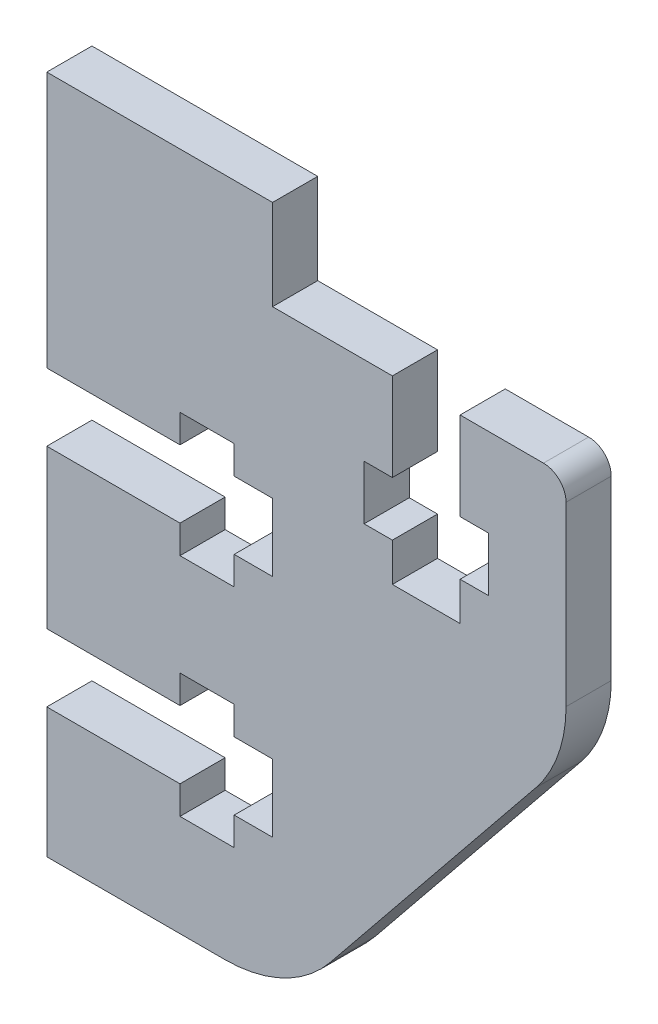
SolidWorks part; units mm, degrees
material "Acrylic (Medium-high impact)"
ref_plane "Front Plane" through (0, 0, 0) normal (0, 0, 1) x (1, 0, 0)
ref_plane "Top Plane" through (0, 0, 0) normal (0, 1, 0) x (1, 0, 0)
ref_plane "Right Plane" through (0, 0, 0) normal (1, 0, 0) x (0, 0, -1)
sketch "Model" plane through (0, 0, 0) normal (0, 0, 1) x (1, 0, 0)
  line L1304 (10, 5.75) -> (8.3, 5.75)
  line L1305 (10, 8.75) -> (8.3, 8.75)
  line L1306 (5.9, 8.75) -> (0, 8.75)
  line L1307 (5.9, 5.75) -> (0, 5.75)
  line L1308 (10, 5.75) -> (10, 8.75)
  line L1309 (10, 26.1) -> (15.306, 26.1)
  line L1310 (18.306, 26.1) -> (22, 26.1)
  line L1311 (21.6642, 13.4853) -> (12.5527, 2.2257)
  line L1312 (23, 25.1) -> (23, 17.2596)
  line L1313 (0, 0) -> (7.8885, 0)
  line L1314 (8.3, 4.5) -> (8.3, 5.75)
  line L1315 (8.3, 8.75) -> (8.3, 10)
  line L1316 (5.9, 4.5) -> (5.9, 5.75)
  line L1317 (5.9, 8.75) -> (5.9, 10)
  line L1318 (8.3, 4.5) -> (5.9, 4.5)
  line L1319 (8.3, 10) -> (5.9, 10)
  line L1320 (10, 15.75) -> (8.3, 15.75)
  line L1321 (10, 18.75) -> (8.3, 18.75)
  line L1322 (5.9, 18.75) -> (0, 18.75)
  line L1323 (5.9, 15.75) -> (0, 15.75)
  line L1324 (10, 15.75) -> (10, 18.75)
  line L1325 (8.3, 14.5) -> (8.3, 15.75)
  line L1326 (8.3, 18.75) -> (8.3, 20)
  line L1327 (5.9, 14.5) -> (5.9, 15.75)
  line L1328 (5.9, 18.75) -> (5.9, 20)
  line L1329 (8.3, 14.5) -> (5.9, 14.5)
  line L1330 (8.3, 20) -> (5.9, 20)
  line L1331 (15.306, 18.1) -> (15.306, 19.8)
  line L1332 (18.306, 18.1) -> (18.306, 19.8)
  line L1333 (18.306, 22.2) -> (18.306, 26.1)
  line L1334 (15.306, 22.2) -> (15.306, 26.1)
  line L1335 (15.306, 18.1) -> (18.306, 18.1)
  line L1336 (14.056, 19.8) -> (15.306, 19.8)
  line L1337 (18.306, 19.8) -> (19.556, 19.8)
  line L1338 (14.056, 22.2) -> (15.306, 22.2)
  line L1339 (18.306, 22.2) -> (19.556, 22.2)
  line L1340 (14.056, 19.8) -> (14.056, 22.2)
  line L1341 (19.556, 19.8) -> (19.556, 22.2)
  line L1342 (10, 30.1) -> (0, 30.1)
  line L1343 (0, 0) -> (0, 5.75)
  line L1344 (0, 8.75) -> (0, 15.75)
  line L1345 (0, 18.75) -> (0, 30.1)
  line L1346 (10, 26.1) -> (10, 30.1)
  arc A520 (23, 25.1) -> (22, 26.1) centre (22, 25.1) ccw
  arc A521 (21.6642, 13.4853) -> (23, 17.2596) centre (17, 17.2596) ccw
  arc A522 (7.8885, 0) -> (12.5527, 2.2257) centre (7.8885, 6) ccw
  dimension "D1" = 1
  dimension "D2" = 6
  dimension "D3" = 6
  dimension "D4" = 5.9
  dimension "D5" = 7.8885
  dimension "D6" = 8.3
  dimension "D7" = 10
  dimension "D8" = 12.5527
  dimension "D9" = 14.056
  dimension "D10" = 15.306
  dimension "D11" = 17
  dimension "D12" = 18.306
  dimension "D13" = 19.556
  dimension "D15" = 4.5
  dimension "D16" = 5.75
  dimension "D18" = 8.75
  dimension "D19" = 10
  dimension "D21" = 14.5
  dimension "D22" = 15.75
  dimension "D24" = 18.1
  dimension "D25" = 18.75
  dimension "D26" = 19.8
  dimension "D27" = 20
  dimension "D28" = 22.2
  dimension "D29" = 26.1
  dimension "D30" = 30.1
extrude "Boss-Extrude1" add sketch "Model" along normal blind 2
